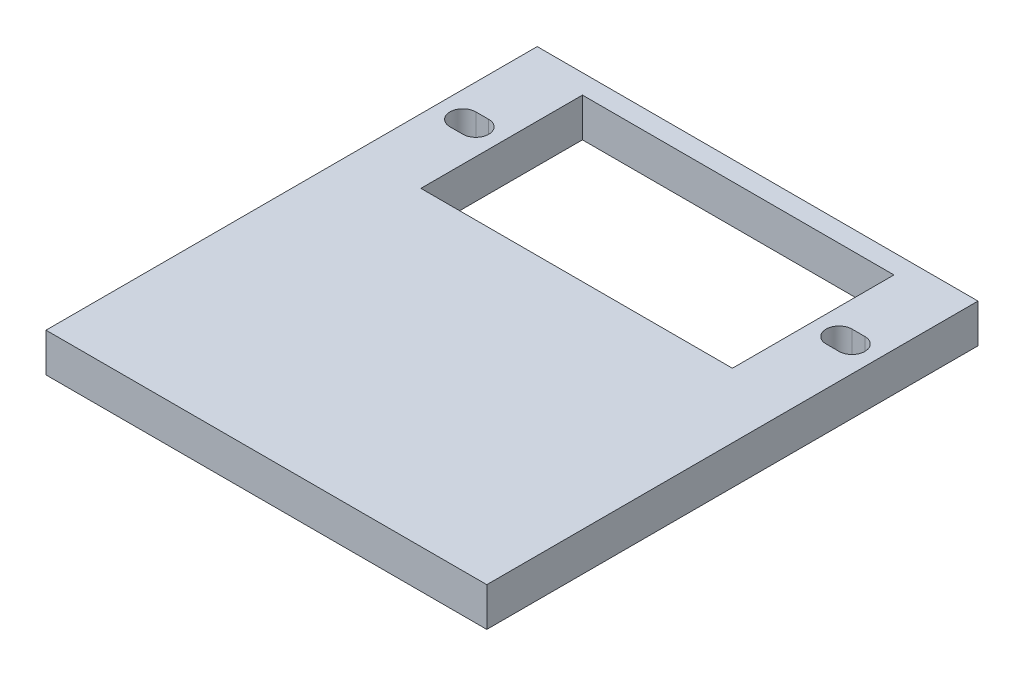
SolidWorks part; units mm, degrees
ref_plane "Plan de face" through (0, 0, 0) normal (0, 0, 1) x (1, 0, 0)
ref_plane "Plan de dessus" through (0, 0, 0) normal (0, 1, 0) x (1, 0, 0)
ref_plane "Plan de droite" through (0, 0, 0) normal (1, 0, 0) x (0, 0, -1)
sketch "Esquisse1" plane through (0, 0, 0) normal (0, 1, 0) x (1, 0, 0)
  line L0 (0, 36.5) -> (-12.05, 36.5)
  line L1 (0, 0) -> (-17.05, 0)
  line L2 (0, 0) -> (0, 38)
  line L3 (0, 38) -> (-17.05, 38)
  line L4 (-17.05, 0) -> (-17.05, 38)
  line L5 (0, 36.5) -> (0, 24)
  line L6 (-12.05, 36.5) -> (-12.05, 24)
  line L7 (0, 24) -> (-12.05, 24)
  line L8 (-15.05, 30.25) -> (-14.05, 30.25) construction
  line L9 (-15.05, 31.25) -> (-14.05, 31.25)
  line L10 (-15.05, 29.25) -> (-14.05, 29.25)
  arc A0 (-15.05, 31.25) -> (-15.05, 29.25) centre (-15.05, 30.25) ccw
  arc A1 (-14.05, 29.25) -> (-14.05, 31.25) centre (-14.05, 30.25) ccw
  point P11 (-14.55, 30.25)
  dimension "D1" = 2
  dimension "D2" = 38
  dimension "D3" = 12.05
  dimension "D4" = 12.5
  dimension "D5" = 24
  dimension "D6" = 6.25
  dimension "D7" = 2
  dimension "D8" = 1
  dimension "D9" = 2
extrude "Boss.-Extru.1" add sketch "Esquisse1" along normal blind 3
mirror "Symétrie1" about plane through (0, 3, 0) normal (-1, 0, 0) of "Boss.-Extru.1"
